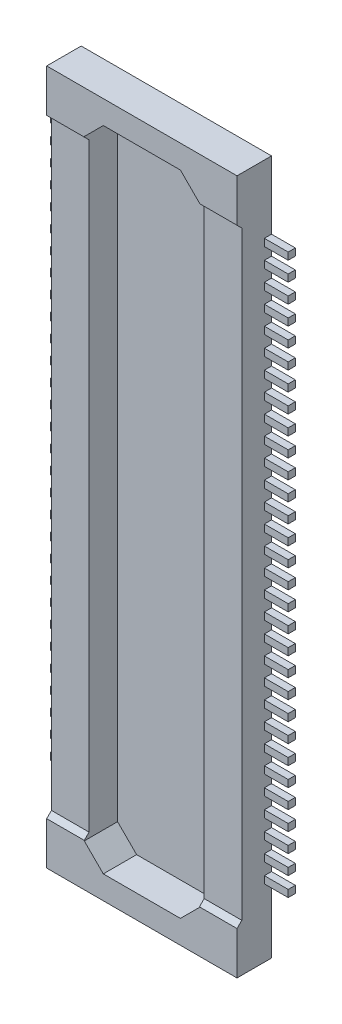
SolidWorks part; units mm, degrees
ref_plane "Plane1" through (0, 0, 0) normal (0, 0, 1) x (1, 0, 0)
ref_plane "Plane2" through (0, 0, 0) normal (0, 1, 0) x (1, 0, 0)
ref_plane "Plane3" through (0, 0, 0) normal (1, 0, 0) x (0, 0, -1)
ref_plane "Plane4" through (0, 0, 0) normal (0, 0, -1) x (-1, 0, 0)
sketch "Sketch1" plane through (0, 0, 0) normal (0, 0, -1) x (-1, 0, 0)
  line L0 (2, -7.3) -> (2, 7.3)
  line L1 (2, 7.3) -> (-2, 7.3)
  line L2 (-2, 7.3) -> (-2, -7.3)
  line L3 (-2, -7.3) -> (2, -7.3)
  line L4 (2, 7.3) -> (-2, -7.3) construction
  dimension "D1" = 4
  dimension "D2" = 14.6
extrude "Extrude1" add sketch "Sketch1" against normal blind 0.725
sketch "Sketch2" plane through (0, 0, 0.725) normal (0, 0, 1) x (1, 0, 0)
  line L0 (-1.21, -6.81) -> (1.21, -6.81)
  line L1 (1.21, -6.81) -> (1.21, 6.81)
  line L2 (1.21, 6.81) -> (-1.21, 6.81)
  line L3 (-1.21, 6.81) -> (-1.21, -6.81)
  line L4 (1.21, 6.81) -> (-1.21, -6.81) construction
  line L5 (2, -7.3) -> (-2, 7.3) construction
  point P8 (0, 0)
  dimension "D1" = 13.62
  dimension "D2" = 2.42
extrude "Cut-Extrude1" cut sketch "Sketch2" against normal blind 0.7
sketch "Sketch3" plane through (-1.21, 0, 0) normal (1, 0, 0) x (0, 0, -1)
  line L0 (-0.725, -6.4) -> (-0.625, -6.3)
  line L1 (-0.625, -6.3) -> (-0.625, 6.3)
  line L2 (-0.625, 6.3) -> (-0.725, 6.4)
  line L3 (-0.725, 6.4) -> (-0.725, -6.4)
  line L4 (-0.725, 7.3) -> (-0.725, -7.3) construction
  line L5 (0, 0) -> (-2.351, 0) construction
  line L6 (0, 7.3) -> (0, -7.3) construction
  line L7 (-0.725, 7.3) -> (0, 7.3) construction
  dimension "D1" = 0.1
  dimension "D2" = 45
  dimension "D3" = 0.9
extrude "Cut-Extrude2" cut sketch "Sketch3" against normal through all and the other way through all
sketch "Sketch29" plane through (-2, 0, 0) normal (-1, 0, 0) x (0, 0, 1)
  line L0 (0.15, 5.725) -> (0, 5.725)
  line L1 (0, 5.725) -> (0, 5.875)
  line L2 (0, 5.875) -> (0.15, 5.875)
  line L3 (0.15, 5.875) -> (0.15, 5.725)
  line L5 (0, -7.3) -> (0, 7.3) construction
  line L6 (0.15, 5.8) -> (0.2418, 5.8) construction
  dimension "D1" = 0.15
  dimension "D2" = 0.15
  dimension "D3" = 5.8
extrude "Extrude26" add sketch "Sketch29" along normal blind 0.5
mirror "Mirror1" about plane through (0, 0, 0) normal (1, 0, 0) of "Extrude26"
chamfer "Chamfer1" distance 0.4 angle 45 1 edges at (-1.21, -6.81, 0.375)
chamfer "Chamfer2" distance 0.4 angle 45 1 edges at (1.21, -6.81, 0.375)
chamfer "Chamfer3" distance 0.4 angle 45 1 edges at (1.21, 6.81, 0.375)
chamfer "Chamfer4" distance 0.4 angle 45 1 edges at (-1.21, 6.81, 0.375)
pattern_linear "LPattern1" count 30 spacing 0.4 along (0, -1, 0) of "Extrude26", "Mirror1"
